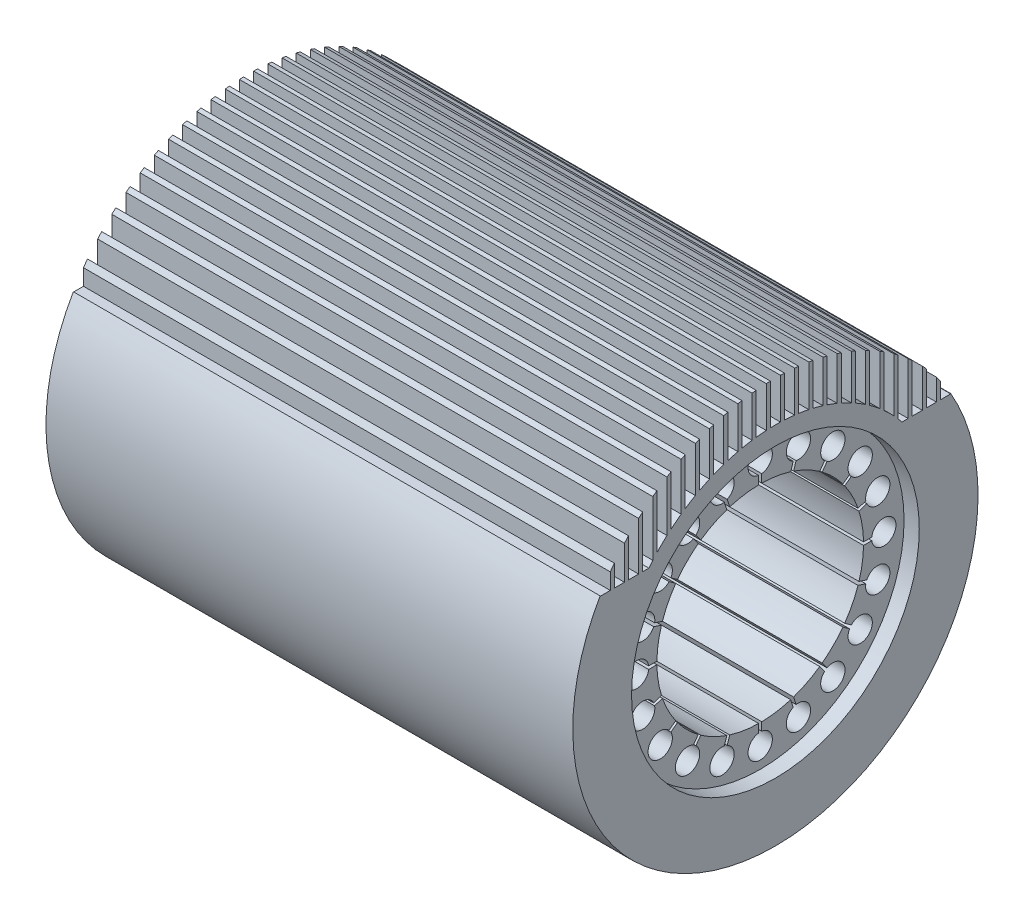
SolidWorks part; units mm, degrees
ref_plane "Front Plane" through (0, 0, 0) normal (0, 0, 1) x (1, 0, 0)
ref_plane "Top Plane" through (0, 0, 0) normal (0, 1, 0) x (1, 0, 0)
ref_plane "Right Plane" through (0, 0, 0) normal (1, 0, 0) x (0, 0, -1)
sketch "Sketch1" plane through (0, 0, 0) normal (0, 0, 1) x (1, 0, 0)
  line L0 (-130, 0) -> (130, 0) construction
  line L2 (-130, 100) -> (130, 100)
  line L4 (122.5, 51) -> (-122.5, 51)
  line L5 (-130, 100) -> (-130, 71)
  line L6 (-130, 71) -> (-122.5, 71)
  line L7 (-122.5, 71) -> (-122.5, 51)
  line L8 (130, 100) -> (130, 71)
  line L9 (130, 71) -> (122.5, 71)
  line L10 (122.5, 71) -> (122.5, 51)
  point P4 (0, 0)
  point P7 (0, 0)
  point P14 (0, 51)
  dimension "D1" = 260
  dimension "D2" = 102
  dimension "D3" = 200
  dimension "D4" = 20
  dimension "D5" = 245
revolve "Revolve1" add sketch "Sketch1" angle 360 about L0
sketch "Sketch2" plane through (-130, 0, 0) normal (-1, 0, 0) x (0, 0, 1)
  line L0 (-0.75, 55.0471) -> (-0.75, 50.9945)
  line L1 (0.75, 55.0471) -> (0.75, 50.9945)
  line L2 (-0.75, 53.0208) -> (0.75, 53.0208) construction
  line L3 (16.2972, 52.5846) -> (15.0449, 48.7304)
  line L4 (17.7238, 52.1211) -> (16.4715, 48.2669)
  line L5 (31.7491, 44.9748) -> (29.367, 41.6962)
  line L6 (32.9626, 44.0932) -> (30.5806, 40.8146)
  line L7 (44.0932, 32.9626) -> (40.8146, 30.5806)
  line L8 (44.9748, 31.7491) -> (41.6962, 29.367)
  line L9 (52.1211, 17.7238) -> (48.2669, 16.4715)
  line L10 (52.5846, 16.2972) -> (48.7304, 15.0449)
  line L11 (55.0471, 0.75) -> (50.9945, 0.75)
  line L12 (55.0471, -0.75) -> (50.9945, -0.75)
  line L13 (52.5846, -16.2972) -> (48.7304, -15.0449)
  line L14 (52.1211, -17.7238) -> (48.2669, -16.4715)
  line L15 (44.9748, -31.7491) -> (41.6962, -29.367)
  line L16 (44.0932, -32.9626) -> (40.8146, -30.5806)
  line L17 (32.9626, -44.0932) -> (30.5806, -40.8146)
  line L18 (31.7491, -44.9748) -> (29.367, -41.6962)
  line L19 (17.7238, -52.1211) -> (16.4715, -48.2669)
  line L20 (16.2972, -52.5846) -> (15.0449, -48.7304)
  line L21 (0.75, -55.0471) -> (0.75, -50.9945)
  line L22 (-0.75, -55.0471) -> (-0.75, -50.9945)
  line L23 (-16.2972, -52.5846) -> (-15.0449, -48.7304)
  line L24 (-17.7238, -52.1211) -> (-16.4715, -48.2669)
  line L25 (-31.7491, -44.9748) -> (-29.367, -41.6962)
  line L26 (-32.9626, -44.0932) -> (-30.5806, -40.8146)
  line L27 (-44.0932, -32.9626) -> (-40.8146, -30.5806)
  line L28 (-44.9748, -31.7491) -> (-41.6962, -29.367)
  line L29 (-52.1211, -17.7238) -> (-48.2669, -16.4715)
  line L30 (-52.5846, -16.2972) -> (-48.7304, -15.0449)
  line L31 (-55.0471, -0.75) -> (-50.9945, -0.75)
  line L32 (-55.0471, 0.75) -> (-50.9945, 0.75)
  line L33 (-52.5846, 16.2972) -> (-48.7304, 15.0449)
  line L34 (-52.1211, 17.7238) -> (-48.2669, 16.4715)
  line L35 (-44.9748, 31.7491) -> (-41.6962, 29.367)
  line L36 (-44.0932, 32.9626) -> (-40.8146, 30.5806)
  line L37 (-32.9626, 44.0932) -> (-30.5806, 40.8146)
  line L38 (-31.7491, 44.9748) -> (-29.367, 41.6962)
  line L39 (-17.7238, 52.1211) -> (-16.4715, 48.2669)
  line L40 (-16.2972, 52.5846) -> (-15.0449, 48.7304)
  circle A0 centre (0, 0) radius 61 construction
  arc A1 (0.75, 55.0471) -> (-0.75, 55.0471) centre (0, 61) ccw
  circle A2 centre (0, 0) radius 51 construction
  arc A3 (0.75, 50.9945) -> (-0.75, 50.9945) centre (0, 0) ccw
  arc A4 (17.7238, 52.1211) -> (16.2972, 52.5846) centre (18.85, 58.0144) ccw
  arc A5 (16.4715, 48.2669) -> (15.0449, 48.7304) centre (0, 0) ccw
  arc A6 (32.9626, 44.0932) -> (31.7491, 44.9748) centre (35.8549, 49.35) ccw
  arc A7 (30.5806, 40.8146) -> (29.367, 41.6962) centre (0, 0) ccw
  arc A8 (44.9748, 31.7491) -> (44.0932, 32.9626) centre (49.35, 35.8549) ccw
  arc A9 (41.6962, 29.367) -> (40.8146, 30.5806) centre (0, 0) ccw
  arc A10 (52.5846, 16.2972) -> (52.1211, 17.7238) centre (58.0144, 18.85) ccw
  arc A11 (48.7304, 15.0449) -> (48.2669, 16.4715) centre (0, 0) ccw
  arc A12 (55.0471, -0.75) -> (55.0471, 0.75) centre (61, 0) ccw
  arc A13 (50.9945, -0.75) -> (50.9945, 0.75) centre (0, 0) ccw
  arc A14 (52.1211, -17.7238) -> (52.5846, -16.2972) centre (58.0144, -18.85) ccw
  arc A15 (48.2669, -16.4715) -> (48.7304, -15.0449) centre (0, 0) ccw
  arc A16 (44.0932, -32.9626) -> (44.9748, -31.7491) centre (49.35, -35.8549) ccw
  arc A17 (40.8146, -30.5806) -> (41.6962, -29.367) centre (0, 0) ccw
  arc A18 (31.7491, -44.9748) -> (32.9626, -44.0932) centre (35.8549, -49.35) ccw
  arc A19 (29.367, -41.6962) -> (30.5806, -40.8146) centre (0, 0) ccw
  arc A20 (16.2972, -52.5846) -> (17.7238, -52.1211) centre (18.85, -58.0144) ccw
  arc A21 (15.0449, -48.7304) -> (16.4715, -48.2669) centre (0, 0) ccw
  arc A22 (-0.75, -55.0471) -> (0.75, -55.0471) centre (0, -61) ccw
  arc A23 (-0.75, -50.9945) -> (0.75, -50.9945) centre (0, 0) ccw
  arc A24 (-17.7238, -52.1211) -> (-16.2972, -52.5846) centre (-18.85, -58.0144) ccw
  arc A25 (-16.4715, -48.2669) -> (-15.0449, -48.7304) centre (0, 0) ccw
  arc A26 (-32.9626, -44.0932) -> (-31.7491, -44.9748) centre (-35.8549, -49.35) ccw
  arc A27 (-30.5806, -40.8146) -> (-29.367, -41.6962) centre (0, 0) ccw
  arc A28 (-44.9748, -31.7491) -> (-44.0932, -32.9626) centre (-49.35, -35.8549) ccw
  arc A29 (-41.6962, -29.367) -> (-40.8146, -30.5806) centre (0, 0) ccw
  arc A30 (-52.5846, -16.2972) -> (-52.1211, -17.7238) centre (-58.0144, -18.85) ccw
  arc A31 (-48.7304, -15.0449) -> (-48.2669, -16.4715) centre (0, 0) ccw
  arc A32 (-55.0471, 0.75) -> (-55.0471, -0.75) centre (-61, 0) ccw
  arc A33 (-50.9945, 0.75) -> (-50.9945, -0.75) centre (0, 0) ccw
  arc A34 (-52.1211, 17.7238) -> (-52.5846, 16.2972) centre (-58.0144, 18.85) ccw
  arc A35 (-48.2669, 16.4715) -> (-48.7304, 15.0449) centre (0, 0) ccw
  arc A36 (-44.0932, 32.9626) -> (-44.9748, 31.7491) centre (-49.35, 35.8549) ccw
  arc A37 (-40.8146, 30.5806) -> (-41.6962, 29.367) centre (0, 0) ccw
  arc A38 (-31.7491, 44.9748) -> (-32.9626, 44.0932) centre (-35.8549, 49.35) ccw
  arc A39 (-29.367, 41.6962) -> (-30.5806, 40.8146) centre (0, 0) ccw
  arc A40 (-16.2972, 52.5846) -> (-17.7238, 52.1211) centre (-18.85, 58.0144) ccw
  arc A41 (-15.0449, 48.7304) -> (-16.4715, 48.2669) centre (0, 0) ccw
  point P7 (0, 53.0208)
  point P110 (0, 0)
  dimension "D1" = 122
  dimension "D2" = 12
  dimension "D3" = 1.5
  dimension "D4" = 20
extrude "Cut-Extrude1" cut sketch "Sketch2" against normal up to next
sketch "Sketch4" plane through (-130, 0, 0) normal (-1, 0, 0) x (0, 0, 1)
  line L0 (9.5, 50) -> (9.5, 110)
  line L1 (2.5, 50) -> (-2.5, 50)
  line L2 (2.5, 50) -> (2.5, 110)
  line L3 (2.5, 110) -> (-2.5, 110)
  line L4 (-2.5, 50) -> (-2.5, 110)
  line L5 (2.5, 50) -> (-2.5, 110) construction
  line L6 (2.5, 110) -> (-2.5, 50) construction
  line L7 (9.5, 50) -> (4.5, 50)
  line L8 (4.5, 50) -> (4.5, 110)
  line L9 (9.5, 110) -> (4.5, 110)
  line L10 (16.5, 50) -> (16.5, 110)
  line L11 (16.5, 50) -> (11.5, 50)
  line L12 (11.5, 50) -> (11.5, 110)
  line L13 (16.5, 110) -> (11.5, 110)
  line L14 (23.5, 50) -> (23.5, 110)
  line L15 (23.5, 50) -> (18.5, 50)
  line L16 (18.5, 50) -> (18.5, 110)
  line L17 (23.5, 110) -> (18.5, 110)
  line L18 (30.5, 50) -> (30.5, 110)
  line L19 (30.5, 50) -> (25.5, 50)
  line L20 (25.5, 50) -> (25.5, 110)
  line L21 (30.5, 110) -> (25.5, 110)
  line L22 (37.5, 50) -> (37.5, 110)
  line L23 (37.5, 50) -> (32.5, 50)
  line L24 (32.5, 50) -> (32.5, 110)
  line L25 (37.5, 110) -> (32.5, 110)
  line L26 (44.5, 50) -> (44.5, 110)
  line L27 (44.5, 50) -> (39.5, 50)
  line L28 (39.5, 50) -> (39.5, 110)
  line L29 (44.5, 110) -> (39.5, 110)
  line L30 (51.5, 50) -> (51.5, 110)
  line L31 (51.5, 50) -> (46.5, 50)
  line L32 (46.5, 50) -> (46.5, 110)
  line L33 (51.5, 110) -> (46.5, 110)
  line L34 (58.5, 50) -> (58.5, 110)
  line L35 (58.5, 50) -> (53.5, 50)
  line L36 (53.5, 50) -> (53.5, 110)
  line L37 (58.5, 110) -> (53.5, 110)
  line L38 (65.5, 50) -> (65.5, 110)
  line L39 (65.5, 50) -> (60.5, 50)
  line L40 (60.5, 50) -> (60.5, 110)
  line L41 (65.5, 110) -> (60.5, 110)
  line L42 (-4.5, 50) -> (-4.5, 110)
  line L43 (-4.5, 50) -> (-9.5, 50)
  line L44 (-9.5, 50) -> (-9.5, 110)
  line L45 (-4.5, 110) -> (-9.5, 110)
  line L46 (-11.5, 50) -> (-11.5, 110)
  line L47 (-11.5, 50) -> (-16.5, 50)
  line L48 (-16.5, 50) -> (-16.5, 110)
  line L49 (-11.5, 110) -> (-16.5, 110)
  line L50 (-18.5, 50) -> (-18.5, 110)
  line L51 (-18.5, 50) -> (-23.5, 50)
  line L52 (-23.5, 50) -> (-23.5, 110)
  line L53 (-18.5, 110) -> (-23.5, 110)
  line L54 (-25.5, 50) -> (-25.5, 110)
  line L55 (-25.5, 50) -> (-30.5, 50)
  line L56 (-30.5, 50) -> (-30.5, 110)
  line L57 (-25.5, 110) -> (-30.5, 110)
  line L58 (-32.5, 50) -> (-32.5, 110)
  line L59 (-32.5, 50) -> (-37.5, 50)
  line L60 (-37.5, 50) -> (-37.5, 110)
  line L61 (-32.5, 110) -> (-37.5, 110)
  line L62 (-39.5, 50) -> (-39.5, 110)
  line L63 (-39.5, 50) -> (-44.5, 50)
  line L64 (-44.5, 50) -> (-44.5, 110)
  line L65 (-39.5, 110) -> (-44.5, 110)
  line L66 (-46.5, 50) -> (-46.5, 110)
  line L67 (-46.5, 50) -> (-51.5, 50)
  line L68 (-51.5, 50) -> (-51.5, 110)
  line L69 (-46.5, 110) -> (-51.5, 110)
  line L70 (-53.5, 50) -> (-53.5, 110)
  line L71 (-53.5, 50) -> (-58.5, 50)
  line L72 (-58.5, 50) -> (-58.5, 110)
  line L73 (-53.5, 110) -> (-58.5, 110)
  line L74 (-60.5, 50) -> (-60.5, 110)
  line L75 (-60.5, 50) -> (-65.5, 50)
  line L76 (-65.5, 50) -> (-65.5, 110)
  line L77 (-60.5, 110) -> (-65.5, 110)
  line L78 (-67.5, 50) -> (-67.5, 110)
  line L79 (-67.5, 50) -> (-72.5, 50)
  line L80 (-72.5, 50) -> (-72.5, 110)
  line L81 (-67.5, 110) -> (-72.5, 110)
  line L82 (-74.5, 50) -> (-74.5, 110)
  line L83 (-74.5, 50) -> (-79.5, 50)
  line L84 (-79.5, 50) -> (-79.5, 110)
  line L85 (-74.5, 110) -> (-79.5, 110)
  line L86 (-81.5, 50) -> (-81.5, 110)
  line L87 (-81.5, 50) -> (-86.5, 50)
  line L88 (-86.5, 50) -> (-86.5, 110)
  line L89 (-81.5, 110) -> (-86.5, 110)
  line L98 (72.5, 50) -> (72.5, 110)
  line L99 (72.5, 50) -> (67.5, 50)
  line L100 (67.5, 50) -> (67.5, 110)
  line L101 (72.5, 110) -> (67.5, 110)
  line L102 (79.5, 50) -> (79.5, 110)
  line L103 (79.5, 50) -> (74.5, 50)
  line L104 (74.5, 50) -> (74.5, 110)
  line L105 (79.5, 110) -> (74.5, 110)
  line L106 (86.5, 50) -> (86.5, 110)
  line L107 (86.5, 50) -> (81.5, 50)
  line L108 (81.5, 50) -> (81.5, 110)
  line L109 (86.5, 110) -> (81.5, 110)
  circle A0 centre (0, 0) radius 80
  circle A1 centre (0, 0) radius 100
  circle A2 centre (0, 0) radius 100
  point P5 (0, 80)
  circle M120 centre (0, 0) radius 100
  dimension "D3" = 60
  dimension "D4" = 5
  dimension "D6" = 2
  dimension "D8" = 2
  dimension "D1" = 0
  dimension "D2" = 20
  dimension "D5" = 13
  dimension "D7" = 13
extrude "Cut-Extrude3" cut sketch "Sketch4" against normal up to next (260 mm away) contours L88 L87 L86 M120 | L84 L83 L82 M120 | A0 L78 L80 M120 | A0 L74 L76 M120 | A0 L70 L72 M120 | A0 L66 L68 M120 | A0 L62 L64 M120 | A0 L58 L60 M120 | A0 L54 L56 M120 | A0 L50 L52 M120 | A0 L46 L48 M120 | A0 L42 L44 M120 | A0 L2 L4 M120 | A0 L0 L8 M120 | A0 L10 L12 M120 | A0 L14 L16 M120 | A0 L18 L20 M120 | A0 L22 L24 M120 | A0 L26 L28 M120 | A0 L30 L32 M120 | A0 L34 L36 M120 | A0 L38 L40 M120 | A0 L98 L100 M120 | L104 L103 L102 M120 | L108 L107 L106 M120
